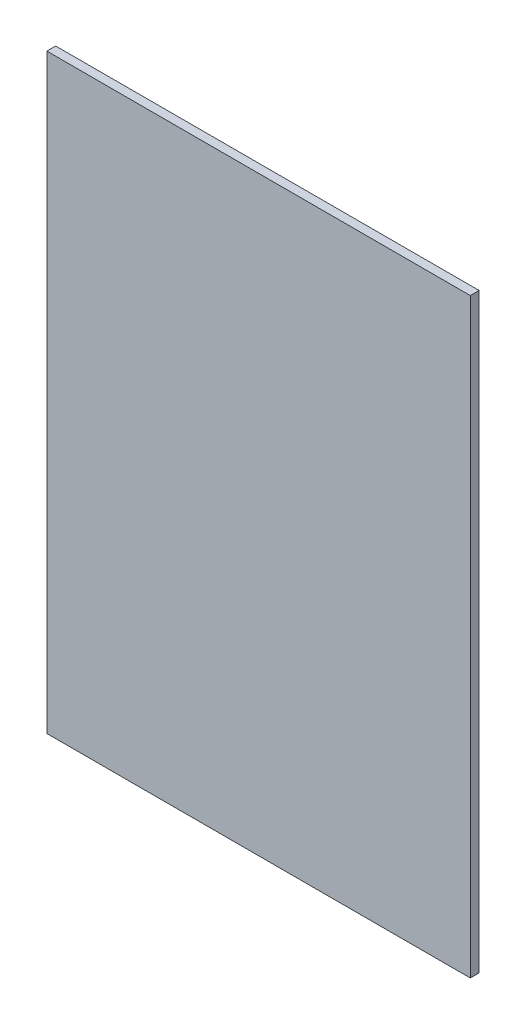
SolidWorks part; units mm, degrees
ref_plane "Plan de face" through (0, 0, 0) normal (0, 0, 1) x (1, 0, 0)
ref_plane "Plan de dessus" through (0, 0, 0) normal (0, 1, 0) x (1, 0, 0)
ref_plane "Plan de droite" through (0, 0, 0) normal (1, 0, 0) x (0, 0, -1)
sketch "Esquisse1" plane through (0, 0, 0) normal (0, 0, 1) x (1, 0, 0)
  line L1 (-290, 335) -> (190, 335)
  line L2 (-290, 335) -> (-290, -335)
  line L3 (-290, -335) -> (190, -335)
  line L4 (190, 335) -> (190, -335)
  dimension "D1" = 480
  dimension "D2" = 670
  dimension "D3" = 335
  dimension "D4" = 190
extrude "Boss.-Extru.1" add sketch "Esquisse1" along normal blind 10
